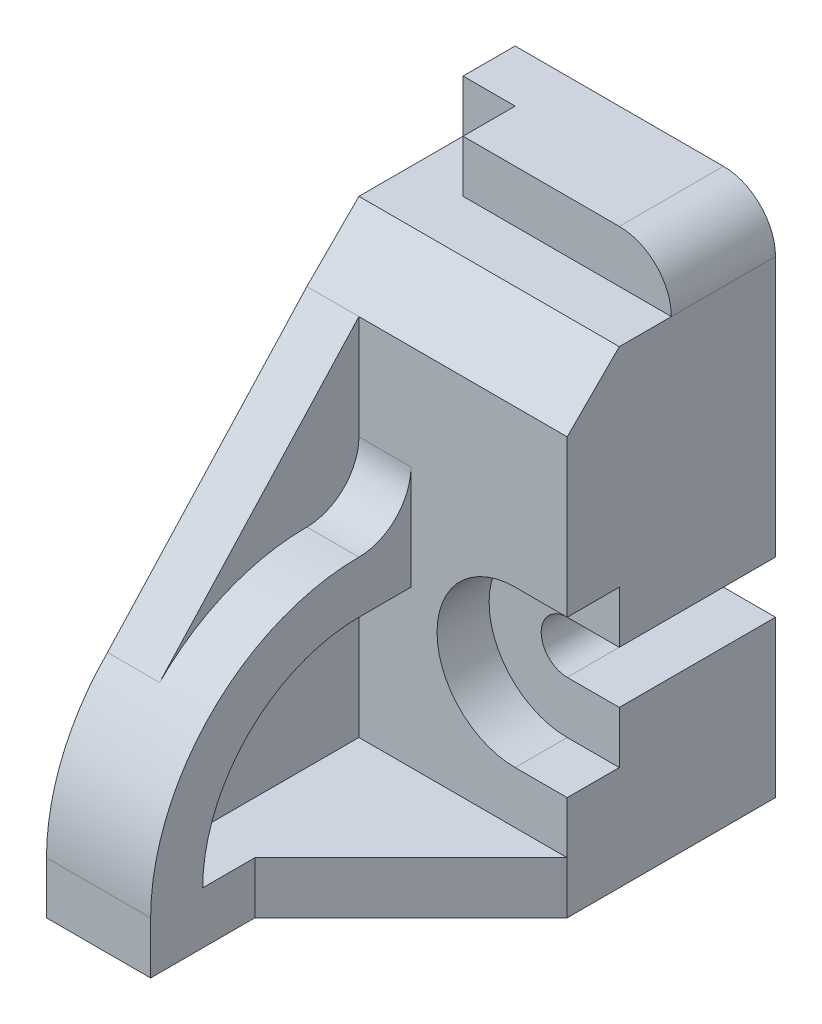
SolidWorks part; units mm, degrees
ref_plane "Front Plane" through (0, 0, 0) normal (0, 0, 1) x (1, 0, 0)
ref_plane "Top Plane" through (0, 0, 0) normal (0, 1, 0) x (1, 0, 0)
ref_plane "Right Plane" through (0, 0, 0) normal (1, 0, 0) x (0, 0, -1)
sketch "Sketch1" plane through (0, 0, 0) normal (0, 0, 1) x (1, 0, 0)
  line L0 (0, 0) -> (0, 9)
  line L1 (0, 9) -> (5, 9)
  line L2 (5, 9) -> (5, 4)
  line L3 (5, 4) -> (4, 4)
  line L4 (4, 3) -> (5, 3)
  line L5 (5, 3) -> (5, 0)
  line L6 (5, 0) -> (0, 0)
  line L7 (0, 9) -> (0, 10)
  line L8 (0, 10) -> (4, 10)
  arc A0 (4, 4) -> (4, 3) centre (4, 3.5) ccw
  arc A1 (5, 9) -> (4, 10) centre (4, 9) ccw
  dimension "D9" = 1
  dimension "D1" = 5
  dimension "D2" = 3
  dimension "D3" = 1
  dimension "D4" = 1
  dimension "D5" = 5
  dimension "D6" = 9
  dimension "D7" = 1
  dimension "D8" = 4
extrude "Boss-Extrude1" add sketch "Sketch1" along normal blind 4 contours L1 A1 L8 L7 | A0 L3 L2 L1 L0 L6 L5 L4
sketch "Sketch2" plane through (0, 0, 4) normal (0, 0, 1) x (1, 0, 0)
  line L0 (5, 3) -> (5, 2)
  line L1 (5, 3) -> (5, 0) construction
  line L2 (5, 2) -> (4, 2)
  line L3 (5, 4) -> (5, 5)
  line L4 (5, 9) -> (5, 4) construction
  line L5 (5, 5) -> (4, 5)
  line L6 (5, 4) -> (4, 4)
  line L7 (5, 3) -> (4, 3)
  arc A0 (4, 5) -> (4, 2) centre (4, 3.5) ccw
  arc A1 (4, 4) -> (4, 3) centre (4, 3.5) ccw
  point P18 (2.5, 3.5)
  dimension "D1" = 1
  dimension "D2" = 1
  dimension "D3" = 1
  dimension "D4" = 1
extrude "Cut-Extrude1" cut sketch "Sketch2" against normal blind 1
sketch "Sketch3" plane through (0, 0, 4) normal (0, 0, 1) x (1, 0, 0)
  line L0 (0, 10) -> (1, 10)
  line L1 (0, 10) -> (4, 10) construction
  line L2 (1, 10) -> (1, 9)
  line L3 (1, 9) -> (0, 9)
  line L4 (0, 0) -> (0, 10) construction
  line L5 (0, 9) -> (0, 10)
  dimension "D1" = 1
  dimension "D2" = 1
extrude "Cut-Extrude2" cut sketch "Sketch3" against normal blind 3
sketch "Sketch4" plane through (0, 0, 0) normal (-1, 0, 0) x (0, 0, 1)
  line L0 (2, 10) -> (2, 9)
  line L1 (1, 10) -> (4, 10) construction
  line L2 (1, 9) -> (4, 9) construction
  line L3 (2, 9) -> (4, 9)
  line L4 (1, 9) -> (4, 9) construction
  line L5 (4, 9) -> (4, 10)
  line L6 (4, 10) -> (2, 10)
  dimension "D1" = 2
  dimension "D2" = 0
extrude "Cut-Extrude4" cut sketch "Sketch4" against normal through all
sketch "Sketch5" plane through (5, 0, 0) normal (1, 0, 0) x (0, 0, -1)
  line L0 (-3, 9) -> (-4, 8)
  line L1 (-4, 9) -> (-2, 9) construction
  line L2 (-4, 9) -> (-4, 5) construction
  line L3 (-4, 8) -> (-4, 9)
  line L4 (-4, 9) -> (-3, 9)
  dimension "D1" = 1
  dimension "D2" = 1
extrude "Cut-Extrude5" cut sketch "Sketch5" against normal through all
sketch "Sketch6" plane through (0, 0, 0) normal (0, -1, 0) x (1, 0, 0)
  line L0 (0, 4) -> (0, 9)
  line L1 (0, 9) -> (2, 9)
  line L2 (2, 9) -> (2, 7)
  line L3 (2, 7) -> (5, 4)
  line L4 (5, 4) -> (0, 4)
  dimension "D1" = 5
  dimension "D2" = 2
  dimension "D3" = 2
extrude "Boss-Extrude2" add sketch "Sketch6" against normal blind 1
sketch "Sketch7" plane through (0, 0, 0) normal (-1, 0, 0) x (0, 0, 1)
  line L0 (4, 8) -> (4, 6)
  line L1 (4, 1) -> (4, 8) construction
  line L2 (9, 1) -> (4, 1) construction
  line L3 (9, 1) -> (4, 1)
  line L4 (4, 1) -> (4, 6)
  line L5 (4, 6) -> (4, 4)
  line L6 (5, 4) -> (4, 4)
  arc A0 (9, 1) -> (5, 5) centre (5, 1) ccw
  arc A1 (4, 6) -> (5, 5) centre (5, 6) ccw
  arc A2 (8, 1) -> (5, 4) centre (5, 1) ccw
  point P5 (5, 1)
  line M8 (9, 1) -> (4, 1)
  dimension "D1" = 2
  dimension "D2" = 1
  dimension "D3" = 2
  dimension "D4" = 1
  dimension "D5" = 1
extrude "Boss-Extrude3" add sketch "Sketch7" against normal blind 2 contours A2 A0 A1 L4 L6 M8
sketch "Sketch9" plane through (0, 0, 0) normal (-1, 0, 0) x (0, 0, 1)
  line L0 (4, 8) -> (7.8284, 3.8284)
  line L1 (4, 8) -> (4, 1)
  line L2 (4, 1) -> (8, 1)
  line L3 (8, 1) -> (7.8284, 3.8284)
  arc A0 (9, 1) -> (5, 5) centre (5, 1) ccw construction
extrude "Boss-Extrude4" add sketch "Sketch9" against normal blind 1
